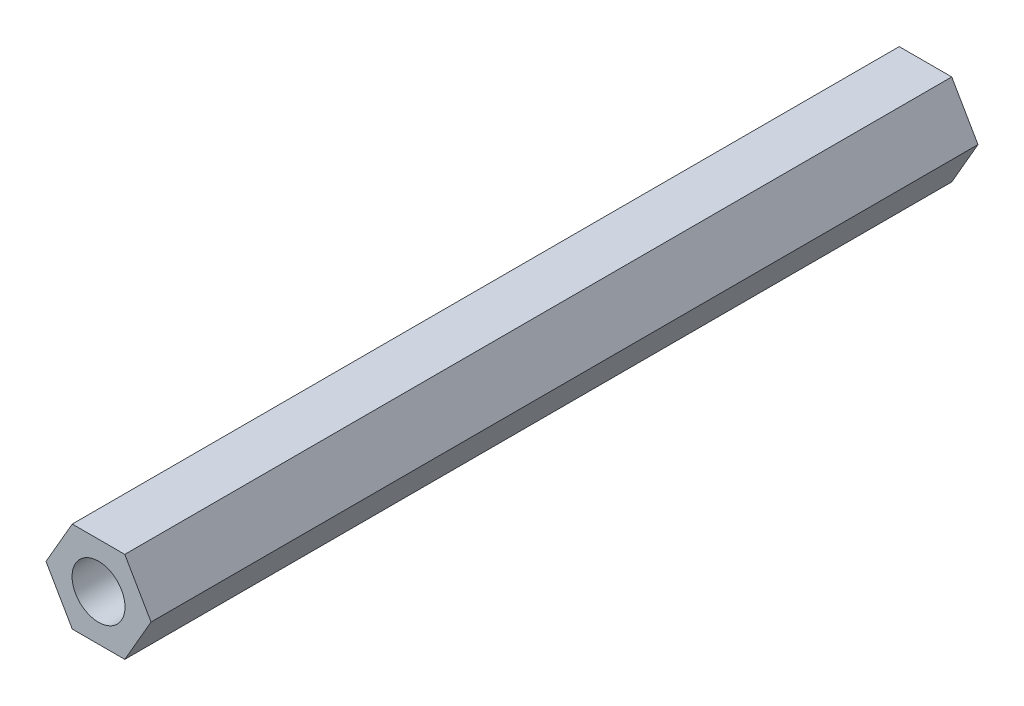
SolidWorks part; units mm, degrees
ref_plane "Front Plane" through (0, 0, 0) normal (0, 0, 1) x (1, 0, 0)
ref_plane "Top Plane" through (0, 0, 0) normal (0, 1, 0) x (1, 0, 0)
ref_plane "Right Plane" through (0, 0, 0) normal (1, 0, 0) x (0, 0, -1)
sketch "Sketch1" plane through (0, 0, 0) normal (0, 0, 1) x (1, 0, 0)
  line L0 (-1.5877, 2.75) -> (1.5877, 2.75)
  line L1 (1.5877, 2.75) -> (3.1754, 0)
  line L2 (3.1754, 0) -> (1.5877, -2.75)
  line L3 (1.5877, -2.75) -> (-1.5877, -2.75)
  line L4 (-1.5877, -2.75) -> (-3.1754, 0)
  line L5 (-3.1754, 0) -> (-1.5877, 2.75)
  circle A0 centre (0, 0) radius 1.6
  point P15 (0, 0)
  point P16 (0, 0)
  point P17 (0, 0)
  point P18 (0, 0)
  point P19 (0, 0)
  point P20 (0, 0)
  dimension "D1" = 3.2
  dimension "D2" = 2.75
  dimension "D3" = 2.75
  dimension "D4" = 3.1754
  dimension "D5" = 120
  dimension "D6" = 120
  dimension "D7" = 1.5877
  dimension "D8" = 1.5877
  dimension "D9" = 3.1754
extrude "Boss-Extrude1" add sketch "Sketch1" along normal blind 50
